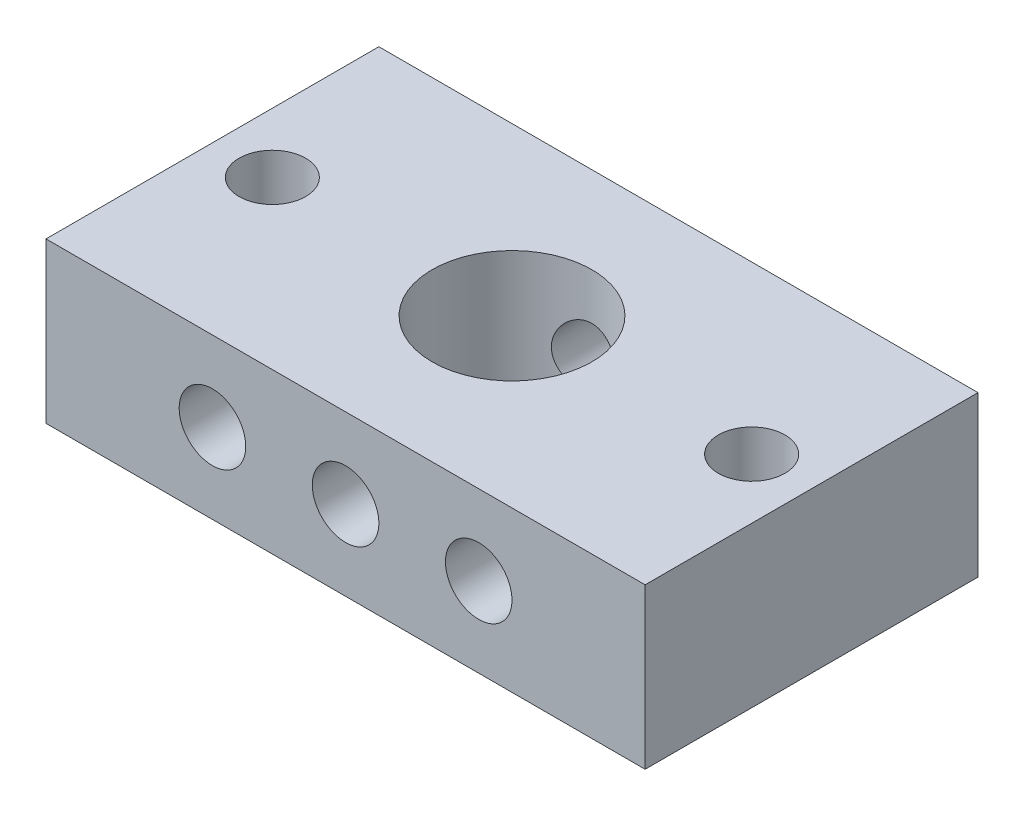
SolidWorks part; units mm, degrees
ref_plane "Front Plane" through (0, 0, 0) normal (0, 0, 1) x (1, 0, 0)
ref_plane "Top Plane" through (0, 0, 0) normal (0, 1, 0) x (1, 0, 0)
ref_plane "Right Plane" through (0, 0, 0) normal (1, 0, 0) x (0, 0, -1)
sketch "Sketch1" plane through (0, 0, 0) normal (0, 1, 0) x (1, 0, 0)
  line L1 (-22.5, 12.5) -> (22.5, 12.5)
  line L2 (-22.5, 12.5) -> (-22.5, -12.5)
  line L3 (-22.5, -12.5) -> (22.5, -12.5)
  line L4 (22.5, 12.5) -> (22.5, -12.5)
  line L5 (-22.5, 12.5) -> (22.5, -12.5) construction
  line L6 (-22.5, -12.5) -> (22.5, 12.5) construction
  point P0 (0, 0)
  dimension "D1" = 25
  dimension "D2" = 45
extrude "Boss-Extrude1" add sketch "Sketch1" along normal blind 12
sketch "Sketch2" plane through (0, 12, 0) normal (0, 1, 0) x (1, 0, 0)
  line L0 (-22.5, -12.5) -> (22.5, -12.5) construction
  line L1 (22.5, 12.5) -> (-22.5, 12.5) construction
  line L2 (-22.5, 12.5) -> (-22.5, -12.5) construction
  line L3 (22.5, -12.5) -> (22.5, 12.5) construction
  circle A0 centre (-18, -7.5) radius 2.5
  circle A1 centre (-18, 7.5) radius 2.5
  circle A2 centre (18, -7.5) radius 2.5
  circle A3 centre (18, 7.5) radius 2.5
  dimension "D1" = 5
  dimension "D2" = 5
  dimension "D3" = 5
  dimension "D4" = 5
  dimension "D5" = 4.5
  dimension "D6" = 4.5
  dimension "D7" = 4.5
  dimension "D8" = 4.5
extrude "Cut-Extrude1" cut sketch "Sketch2" against normal blind 12
sketch "Sketch3" plane through (0, 0, -12.5) normal (0, 0, -1) x (-1, 0, 0)
  circle A0 centre (0, 6) radius 2.5
extrude "Cut-Extrude2" cut sketch "Sketch3" against normal blind 72
sketch "Sketch4" plane through (0, 0, -12.5) normal (0, 0, -1) x (-1, 0, 0)
  line L0 (-22.5, 12) -> (22.5, 12) construction
  circle A0 centre (10, 6) radius 2.5
  circle A1 centre (-10, 6) radius 2.5
  circle A2 centre (0, 6) radius 2.5 construction
  point P6 (0, 12)
  dimension "D1" = 10
  dimension "D2" = 10
extrude "Cut-Extrude3" cut sketch "Sketch4" against normal blind 72
sketch "Sketch5" plane through (0, 12, 0) normal (0, 1, 0) x (1, 0, 0)
  circle A0 centre (0, 0) radius 6
extrude "Cut-Extrude4" cut sketch "Sketch5" against normal blind 72
sketch "Sketch6" plane through (0, 12, 0) normal (0, 1, 0) x (1, 0, 0)
  circle A0 centre (-18, 0) radius 2.5
  circle A1 centre (18, 0) radius 2.5
extrude "Cut-Extrude5" cut sketch "Sketch6" against normal blind 72
sketch "Sketch7" plane through (0, 12, 0) normal (0, 1, 0) x (1, 0, 0)
  circle A0 centre (18, -7.5) radius 2.5
  circle A1 centre (18, 7.5) radius 2.5
  circle A2 centre (-18, -7.5) radius 2.5
  circle A3 centre (-18, 7.5) radius 2.5
extrude "Boss-Extrude2" add sketch "Sketch7" against normal up to surface (12 mm away) up to face at (-18, 0, 2.5)
